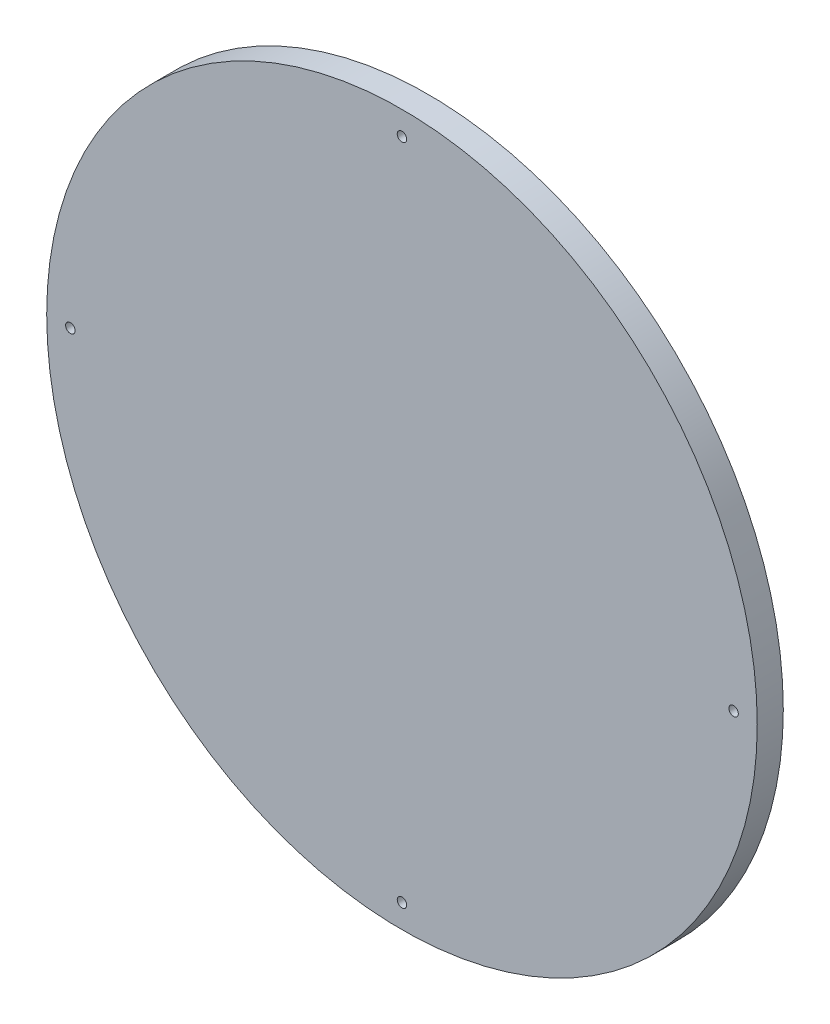
SolidWorks part; units mm, degrees
ref_plane "Plan de face" through (0, 0, 0) normal (0, 0, 1) x (1, 0, 0)
ref_plane "Plan de dessus" through (0, 0, 0) normal (0, 1, 0) x (1, 0, 0)
ref_plane "Plan de droite" through (0, 0, 0) normal (1, 0, 0) x (0, 0, -1)
sketch "Esquisse1" plane through (0, 0, 0) normal (0, 0, 1) x (1, 0, 0)
  circle A0 centre (0, 0) radius 300
extrude "Boss.-Extru.1" add sketch "Esquisse1" along normal blind 22
sketch "Esquisse2" plane through (0, 0, 22) normal (0, 0, 1) x (1, 0, 0)
  circle A0 centre (0, 280) radius 4
  dimension "D1" = 280
extrude "Enlèv. mat.-Extru.1" cut sketch "Esquisse2" against normal through all
sketch "Esquisse3" plane through (0, 0, 0) normal (1, 0, 0) x (0, 0, -1)
  line L0 (133.9123, 0) -> (-227.7324, 0) construction
pattern_circular "Répétition circulaire1" count 4 every 90 about axis through (0, 0, 0) along (0, 0, 1) of "Enlèv. mat.-Extru.1"
sketch "Esquisse4" plane through (0, 0, 0) normal (0, 0, -1) x (-1, 0, 0)
  circle A0 centre (0, 280) radius 12 construction
  circle A1 centre (0, 280) radius 12
extrude "Enlèv. mat.-Extru.2" cut sketch "Esquisse4" against normal blind 5
